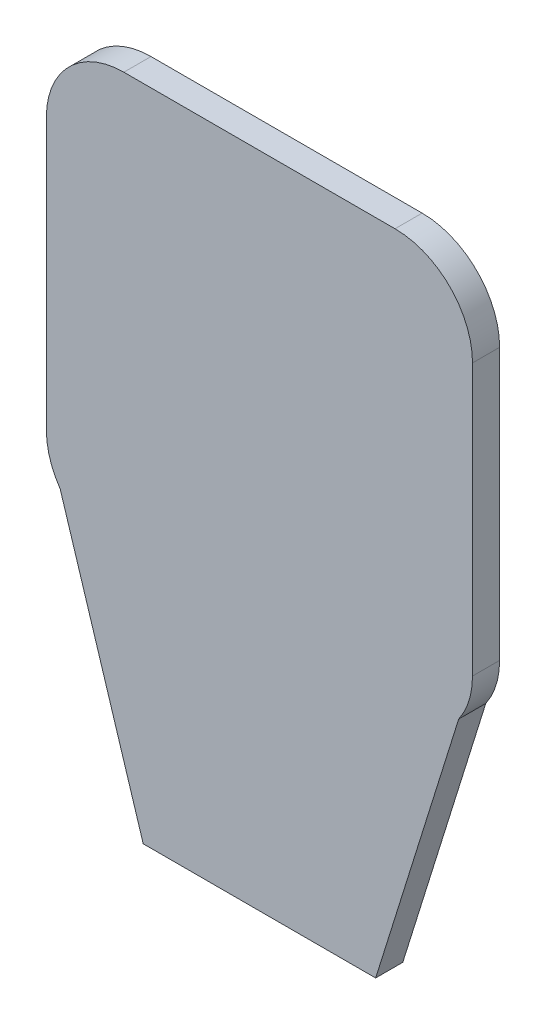
SolidWorks part; units mm, degrees
ref_plane "Alzado" through (0, 0, 0) normal (0, 0, 1) x (1, 0, 0)
ref_plane "Planta" through (0, 0, 0) normal (0, 1, 0) x (1, 0, 0)
ref_plane "Vista lateral" through (0, 0, 0) normal (1, 0, 0) x (0, 0, -1)
sketch "Croquis1" plane through (0, 0, 0) normal (0, 0, 1) x (1, 0, 0)
  line L0 (-16.9077, -60.7083) -> (13.0923, -60.7083)
  line L1 (-19.4077, 24.2917) -> (15.5923, 24.2917)
  line L2 (-29.4077, 14.2917) -> (-29.4077, -20.7083)
  line L4 (25.5923, 14.2917) -> (25.5923, -20.7083)
  line L5 (-29.4077, 24.2917) -> (25.5923, -30.7083) construction
  line L6 (-29.4077, -30.7083) -> (25.5923, 24.2917) construction
  line L7 (13.0923, -60.7083) -> (23.8082, -26.4092)
  line L8 (-16.9077, -60.7083) -> (-27.6235, -26.4092)
  arc A0 (15.5923, 24.2917) -> (25.5923, 14.2917) centre (15.5923, 14.2917) cw
  arc A1 (23.8082, -26.4092) -> (25.5923, -20.7083) centre (15.5923, -20.7083) ccw
  arc A2 (-29.4077, -20.7083) -> (-27.6235, -26.4092) centre (-19.4077, -20.7083) ccw
  arc A3 (-19.4077, 24.2917) -> (-29.4077, 14.2917) centre (-19.4077, 14.2917) ccw
  point P0 (-1.9077, -3.2083)
  dimension "D3" = 10
  dimension "D1" = 55
  dimension "D2" = 55
  dimension "D4" = 30
  dimension "D6" = 107.35
  dimension "D7" = 107.35
extrude "Saliente-Extruir1" add sketch "Croquis1" along normal blind 3.5
